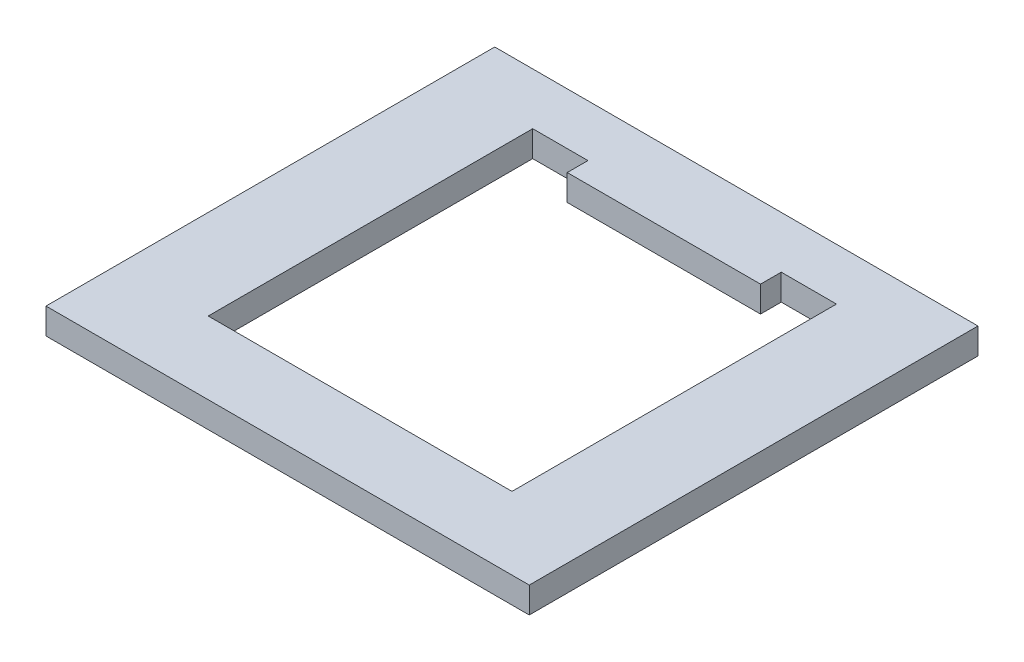
SolidWorks part; units mm, degrees
ref_plane "Piano frontale" through (0, 0, 0) normal (0, 0, 1) x (1, 0, 0)
ref_plane "Piano superiore" through (0, 0, 0) normal (0, 1, 0) x (1, 0, 0)
ref_plane "Piano destro" through (0, 0, 0) normal (1, 0, 0) x (0, 0, -1)
sketch "Schizzo1" plane through (0, 0, 0) normal (0, 1, 0) x (1, 0, 0)
  line L0 (-22, 22) -> (-22, 25)
  line L1 (-35, 32.5) -> (35, 32.5)
  line L2 (-35, 32.5) -> (-35, -32.5)
  line L3 (-35, -32.5) -> (35, -32.5)
  line L4 (35, 32.5) -> (35, -32.5)
  line L5 (-35, 32.5) -> (35, -32.5) construction
  line L6 (-35, -32.5) -> (35, 32.5) construction
  line L7 (-22, 22) -> (22, 22)
  line L8 (-22, 22) -> (-22, -22)
  line L9 (-22, -22) -> (22, -22)
  line L10 (22, 22) -> (22, -22)
  line L11 (-22, 22) -> (22, -22) construction
  line L12 (-22, -22) -> (22, 22) construction
  line L13 (-22, 25) -> (-14, 25)
  line L14 (-14, 25) -> (-14, 22)
  line L15 (22, 22) -> (22, 25)
  line L16 (22, 25) -> (14, 25)
  line L17 (14, 25) -> (14, 22)
  point P0 (0, 0)
  point P5 (0, 0)
  dimension "D1" = 70
  dimension "D2" = 65
  dimension "D3" = 44
  dimension "D4" = 8
  dimension "D5" = 3
extrude "Estrusione-Estrusione1" add sketch "Schizzo1" along normal blind 3.76 contours L4 L1 L2 L3 L17 L16 L15 L10 L9 L8 L0 L13 L14 L7
